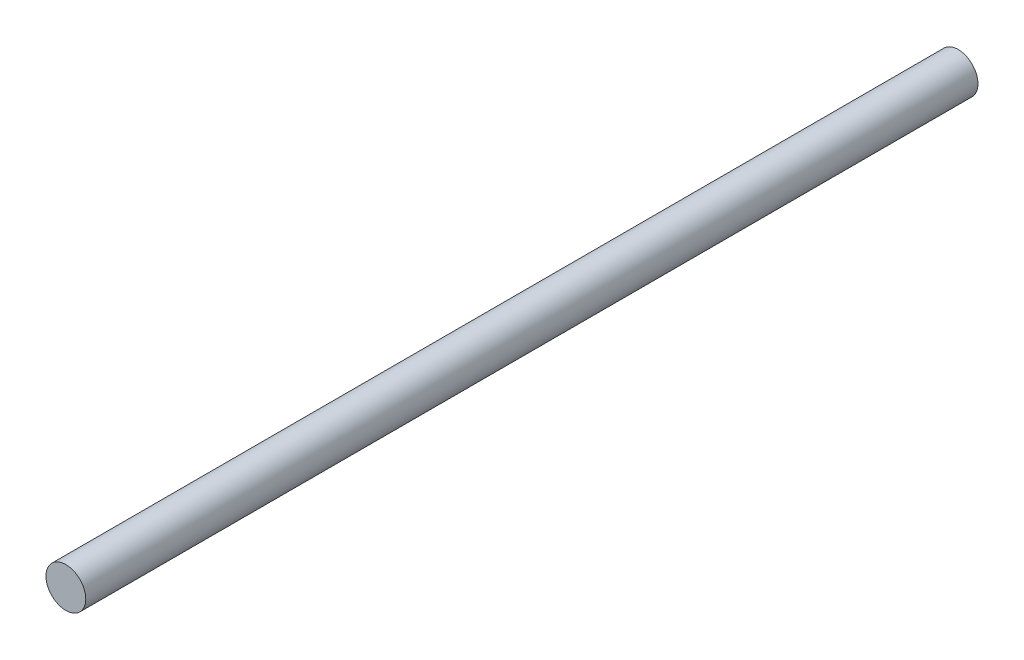
SolidWorks part; units mm, degrees
ref_plane "Front Plane" through (0, 0, 0) normal (0, 0, 1) x (1, 0, 0)
ref_plane "Top Plane" through (0, 0, 0) normal (0, 1, 0) x (1, 0, 0)
ref_plane "Right Plane" through (0, 0, 0) normal (1, 0, 0) x (0, 0, -1)
sketch "Sketch1" plane through (0, 0, 0) normal (0, 0, 1) x (1, 0, 0)
  circle A0 centre (0, 0) radius 6
  dimension "D1" = 12
extrude "Boss-Extrude1" add sketch "Sketch1" along normal blind 269
